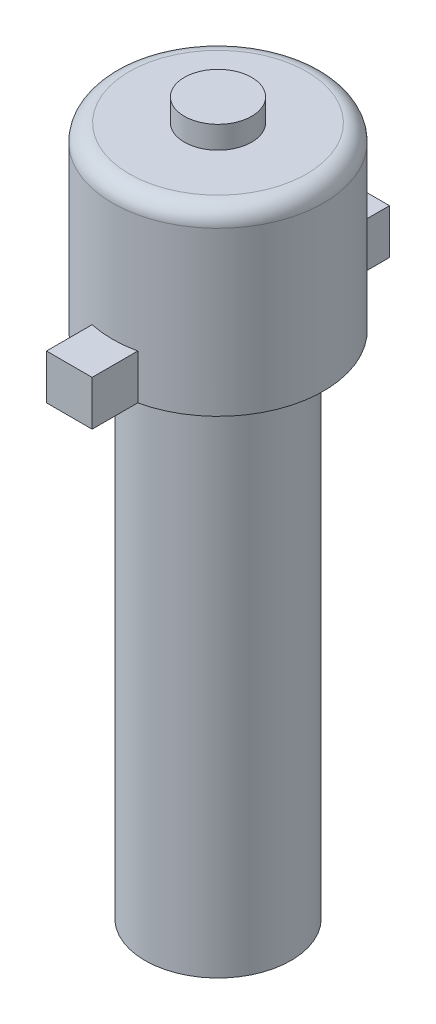
SolidWorks part; units mm, degrees
ref_plane "Front Plane" through (0, 0, 0) normal (0, 0, 1) x (1, 0, 0)
ref_plane "Top Plane" through (0, 0, 0) normal (0, 1, 0) x (1, 0, 0)
ref_plane "Right Plane" through (0, 0, 0) normal (1, 0, 0) x (0, 0, -1)
sketch "Sketch1" plane through (0, 0, 0) normal (0, 1, 0) x (1, 0, 0)
  circle A0 centre (0, 0) radius 3.25
  dimension "D1" = 6.5
extrude "Boss-Extrude1" add sketch "Sketch1" along normal blind 22.686 contours A0
sketch "Sketch2" plane through (0, 0, 0) normal (0, -1, 0) x (1, 0, 0)
  circle A1 centre (0, 0) radius 1.75
  dimension "D1" = 3.5
extrude "Cut-Extrude1" [suppressed] cut sketch "Sketch2" against normal blind 2.5
sketch "Sketch6" plane through (0, 22.686, 0) normal (0, 1, 0) x (1, 0, 0)
  circle A0 centre (0, 0) radius 4.7
  dimension "D1" = 9.4
extrude "Boss-Extrude2" add sketch "Sketch6" along normal blind 8 contours A0
fillet "Fillet2" radius 0.75 1 edges at (0, 30.686, 4.7)
sketch "Sketch7" plane through (0, 30.686, 0) normal (0, 1, 0) x (1, 0, 0)
  circle A0 centre (0, 0) radius 1.5
  dimension "D1" = 3
extrude "Boss-Extrude3" add sketch "Sketch7" along normal blind 1
sketch "Sketch8" plane through (0, 22.686, 0) normal (0, -1, 0) x (1, 0, 0)
  line L0 (0, 4.7) -> (0, -4.7) construction
  line L1 (-1.016, 4.5889) -> (-1.016, 6.6209)
  line L2 (-1.016, 6.6209) -> (1.016, 6.6209)
  line L3 (1.016, 6.6209) -> (1.016, 4.5889)
  line L4 (-4.7, 0) -> (4.7, 0) construction
  line L5 (1.016, -6.6209) -> (1.016, -4.5889)
  line L6 (-1.016, -6.6209) -> (1.016, -6.6209)
  line L7 (-1.016, -4.5889) -> (-1.016, -6.6209)
  circle A0 centre (0, 0) radius 4.7 construction
  arc A1 (1.016, -4.5889) -> (-1.016, -4.5889) centre (0, 0) cw
  circle A2 centre (0, 0) radius 4.7
  arc A3 (1.016, 4.5889) -> (-1.016, 4.5889) centre (0, 0) ccw
  dimension "D2" = 2.032
  dimension "D3" = 2.032
  dimension "D1" = 0
extrude "Boss-Extrude4" add sketch "Sketch8" against normal blind 2
